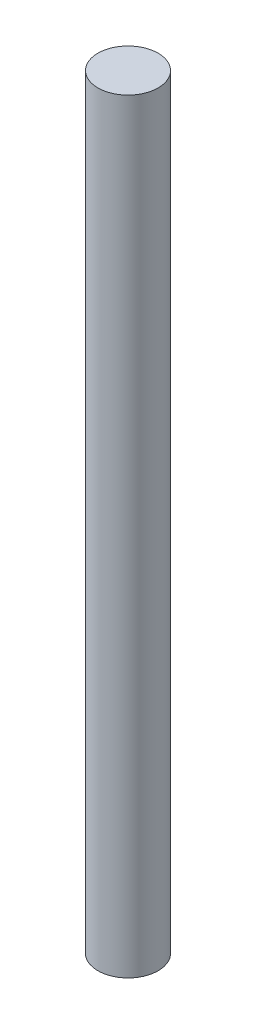
SolidWorks part; units mm, degrees
material "6061 Alloy"
ref_plane "Front Plane" through (0, 0, 0) normal (0, 0, 1) x (1, 0, 0)
ref_plane "Top Plane" through (0, 0, 0) normal (0, 1, 0) x (1, 0, 0)
ref_plane "Right Plane" through (0, 0, 0) normal (1, 0, 0) x (0, 0, -1)
sketch "Sketch1" plane through (0, 0, 0) normal (0, 1, 0) x (1, 0, 0)
  circle A0 centre (0, 0) radius 6
  dimension "D1" = 12
extrude "Boss-Extrude1" add sketch "Sketch1" along normal blind 304.8
sketch "Sketch2" plane through (0, 0, 0) normal (0, -1, 0) x (1, 0, 0)
  circle A0 centre (0, 0) radius 11.262
extrude "Cut-Extrude1" cut sketch "Sketch2" against normal blind 152.4
